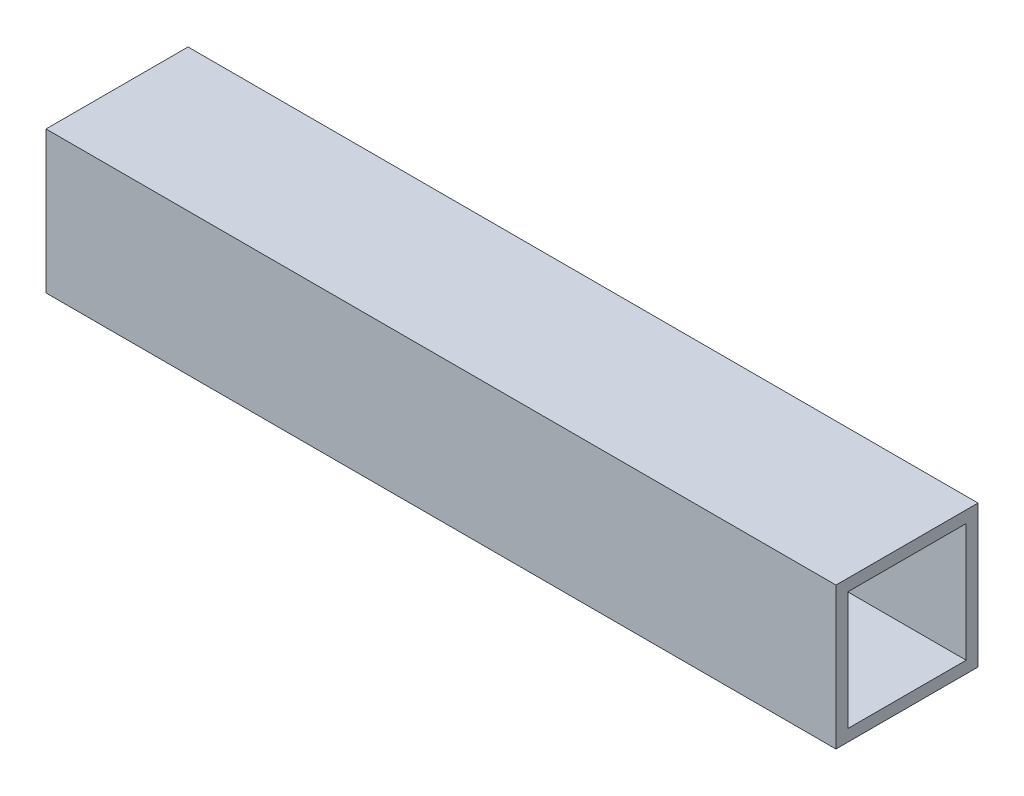
SolidWorks part; units mm, degrees
material "AISI 1020"
ref_plane "Front Plane" through (0, 0, 0) normal (0, 0, 1) x (1, 0, 0)
ref_plane "Top Plane" through (0, 0, 0) normal (0, 1, 0) x (1, 0, 0)
ref_plane "Right Plane" through (0, 0, 0) normal (1, 0, 0) x (0, 0, -1)
sketch "Sketch1" plane through (0, 0, 0) normal (0, 0, 1) x (1, 0, 0)
  line L1 (0, 0) -> (211.9, 0)
  line L2 (0, 0) -> (0, 38.1)
  line L3 (0, 38.1) -> (211.9, 38.1)
  line L4 (211.9, 0) -> (211.9, 38.1)
  dimension "D1" = 211.9
  dimension "D2" = 38.1
extrude "Boss-Extrude1" add sketch "Sketch1" against normal blind 38.1
sketch "Sketch2" plane through (211.9, 0, 0) normal (1, 0, 0) x (0, 0, -1)
  line L1 (38.1, 38.1) -> (0, 38.1) construction
  line L2 (38.1, 38.1) -> (38.1, 0) construction
  line L3 (38.1, 0) -> (0, 0) construction
  line L4 (0, 38.1) -> (0, 0) construction
  line L5 (34.925, 3.175) -> (3.175, 3.175)
  line L6 (34.925, 3.175) -> (34.925, 34.925)
  line L7 (34.925, 34.925) -> (3.175, 34.925)
  line L8 (3.175, 3.175) -> (3.175, 34.925)
  line L9 (34.925, 3.175) -> (3.175, 34.925) construction
  line L10 (34.925, 34.925) -> (3.175, 3.175) construction
  point P6 (0, 19.05)
  point P7 (19.05, 38.1)
  point P8 (19.05, 19.05)
  point P9 (19.05, 19.05)
  dimension "D1" = 3.175
extrude "Cut-Extrude1" cut sketch "Sketch2" against normal through all both and the other way through all contours L6 L5 L8 L7
